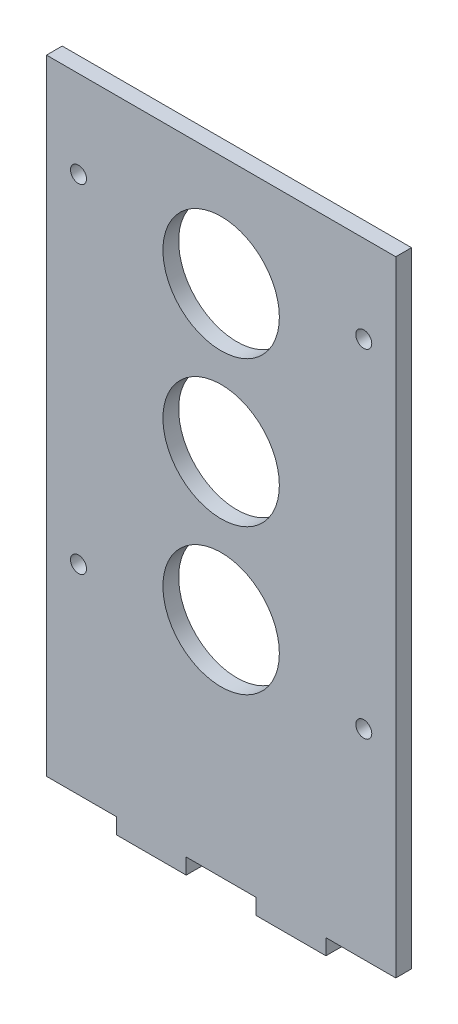
SolidWorks part; units mm, degrees
ref_plane "Ön Düzlem" through (0, 0, 0) normal (0, 0, 1) x (1, 0, 0)
ref_plane "Üst Düzlem" through (0, 0, 0) normal (0, 1, 0) x (1, 0, 0)
ref_plane "Sağ Düzlem" through (0, 0, 0) normal (1, 0, 0) x (0, 0, -1)
sketch "Sketch1" plane through (0, 0, 0) normal (0, 0, 1) x (1, 0, 0)
  line L2 (30, -47.3) -> (30, 50)
  line L4 (-30, -47.3) -> (-30, 50)
  line L5 (-30, 50) -> (-30, 60)
  line L6 (-30, 60) -> (30, 60)
  line L7 (30, 60) -> (30, 50)
  line L11 (18, -50) -> (6, -50)
  line L13 (-6, -50) -> (-18, -50)
  line L15 (-18, -50) -> (-18, -47.3)
  line L16 (-18, -47.3) -> (-30, -47.3)
  line L17 (-6, -50) -> (-6, -47.3)
  line L18 (-6, -47.3) -> (6, -47.3)
  line L19 (6, -50) -> (6, -47.3)
  line L20 (18, -50) -> (18, -47.3)
  line L21 (18, -47.3) -> (30, -47.3)
  circle A0 centre (-24.5, 45) radius 1.375
  circle A1 centre (24.5, 45) radius 1.375
  circle A2 centre (-24.5, -13) radius 1.375
  circle A3 centre (24.5, -13) radius 1.375
  circle A4 centre (0, 16) radius 10
  circle A5 centre (0, 41) radius 10
  circle A6 centre (0, -9) radius 10
  point P0 (0, 0)
  point P30 (0, 0)
extrude "Boss-Extrude1" add sketch "Sketch1" along normal blind 2.7
